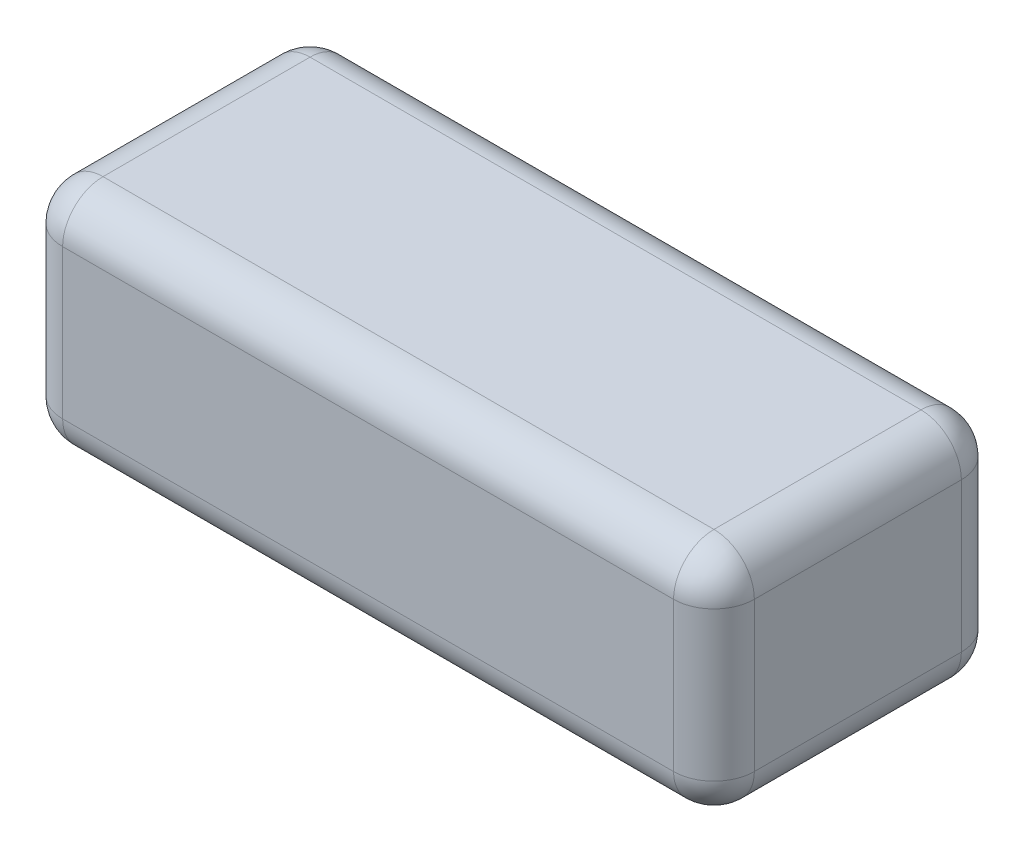
SolidWorks part; units mm, degrees
ref_plane "Front Plane" through (0, 0, 0) normal (0, 0, 1) x (1, 0, 0)
ref_plane "Top Plane" through (0, 0, 0) normal (0, 1, 0) x (1, 0, 0)
ref_plane "Right Plane" through (0, 0, 0) normal (1, 0, 0) x (0, 0, -1)
sketch "Sketch1" plane through (0, 0, 0) normal (0, 1, 0) x (1, 0, 0)
  line L0 (0, 28.5) -> (0, 0) construction
  line L1 (-68.5, -28.5) -> (68.5, -28.5)
  line L2 (-68.5, -28.5) -> (-68.5, 28.5)
  line L3 (-68.5, 28.5) -> (68.5, 28.5)
  line L4 (68.5, -28.5) -> (68.5, 28.5)
  line L5 (0, 0) -> (68.5, 0) construction
  line L7 (62.3453, 14.8462) -> (29.5851, 4.6762)
  point P7 (0, 0)
  dimension "D1" = 57
  dimension "D2" = 137
extrude "Boss-Extrude1" add sketch "Sketch1" along normal blind 45.54
fillet "Fillet1" radius 8 12 edges at (-68.5, 22.77, 28.5) (68.5, 22.77, 28.5) (68.5, 22.77, -28.5) (-68.5, 22.77, -28.5) (0, 45.54, -28.5) (68.5, 45.54, 0) (0, 45.54, 28.5) (-68.5, 45.54, 0) (0, 0, -28.5) (68.5, 0, 0) (0, 0, 28.5) (-68.5, 0, 0)
